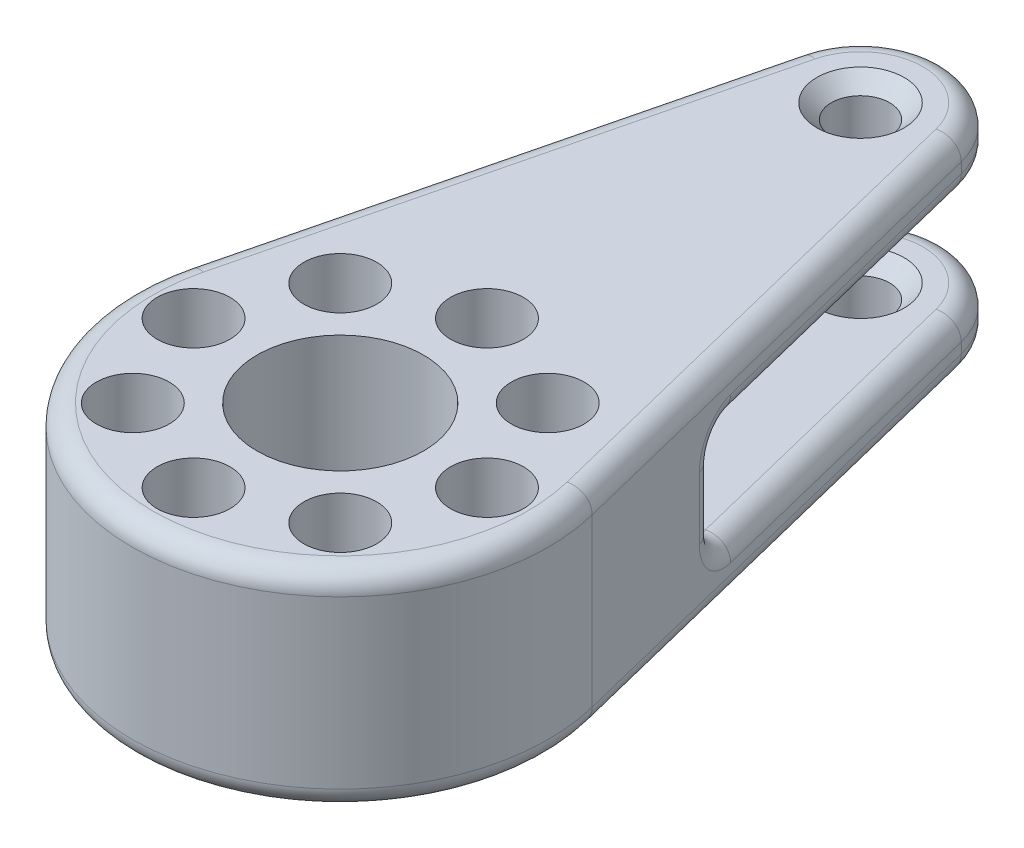
SolidWorks part; units mm, degrees
ref_plane "Front Plane" through (0, 0, 0) normal (0, 0, 1) x (1, 0, 0)
ref_plane "Top Plane" through (0, 0, 0) normal (0, 1, 0) x (1, 0, 0)
ref_plane "Right Plane" through (0, 0, 0) normal (1, 0, 0) x (0, 0, -1)
sketch "Sketch1" plane through (0, 0, 0) normal (0, 1, 0) x (1, 0, 0)
  line L0 (-9.7077, 2.4) -> (-3.8831, 25.96)
  line L1 (3.8831, 25.96) -> (9.7077, 2.4)
  arc A0 (-9.7077, 2.4) -> (9.7077, 2.4) centre (0, 0) ccw
  arc A1 (3.8831, 25.96) -> (-3.8831, 25.96) centre (0, 25) ccw
  circle A2 centre (0, 25) radius 1.4
  circle A11 centre (0, 0) radius 4
  dimension "D1" = 25
  dimension "D2" = 20
  dimension "D3" = 8
  dimension "D4" = 2.8
  dimension "D8" = 8
extrude "Boss-Extrude1" add sketch "Sketch1" along normal mid plane 10
sketch "Sketch2" plane through (0, 0, 0) normal (0, 1, 0) x (1, 0, 0)
  circle A0 centre (0, 7.05) radius 0.75
  dimension "D1" = 1.5
  dimension "D2" = 7.05
extrude "Cut-Extrude1" cut sketch "Sketch2" along normal through all both and the other way through all
sketch "Sketch4" plane through (0, 0, 0) normal (0, 1, 0) x (1, 0, 0)
  circle A0 centre (0, 7.05) radius 1.75
  dimension "D1" = 3.5
extrude "Cut-Extrude2" cut sketch "Sketch4" along normal through all and the other way offset from surface (4 mm away) 1 other way up to face at (0, -5, -6.3)
pattern_circular "CirPattern1" count 8 over 360 about axis through (0, 0, 0) along (0, 1, 0) of "Cut-Extrude1", "Cut-Extrude2"
sketch "Sketch5" plane through (0, 0, 0) normal (0, 1, 0) x (1, 0, 0)
  line L0 (-7.8288, 10) -> (7.8288, 10)
  line L1 (-9.7077, 2.4) -> (-3.8831, 25.96) construction
  line L2 (3.8831, 25.96) -> (9.7077, 2.4) construction
  line L3 (3.8831, 25.96) -> (7.8288, 10)
  line L4 (-7.8288, 10) -> (-3.8831, 25.96)
  arc A0 (3.8831, 25.96) -> (-3.8831, 25.96) centre (0, 25) ccw construction
  arc A1 (3.8831, 25.96) -> (-3.8831, 25.96) centre (0, 25) ccw
  dimension "D1" = 10
extrude "Cut-Extrude3" cut sketch "Sketch5" along normal mid plane 5
fillet "Fillet1" radius 1 18 edges at (0, -2.5, -29) (0, 2.5, -29) (-5.856, 2.5, -17.98) (-5.856, -2.5, -17.98) (5.856, -2.5, -17.98) (5.856, 2.5, -17.98) (-7.8288, 0, -10) (0, -2.5, -10) (7.8288, 0, -10) (0, 2.5, -10) (0, 5, 10) (-6.7954, 5, -14.18) (0, 5, -29) (6.7954, 5, -14.18) (0, -5, -29) (-6.7954, -5, -14.18) (0, -5, 10) (6.7954, -5, -14.18)
chamfer "Chamfer1" distance 0.7 angle 45 2 edges at (0, -2.5, -23.6) (0, 5, -23.6)
